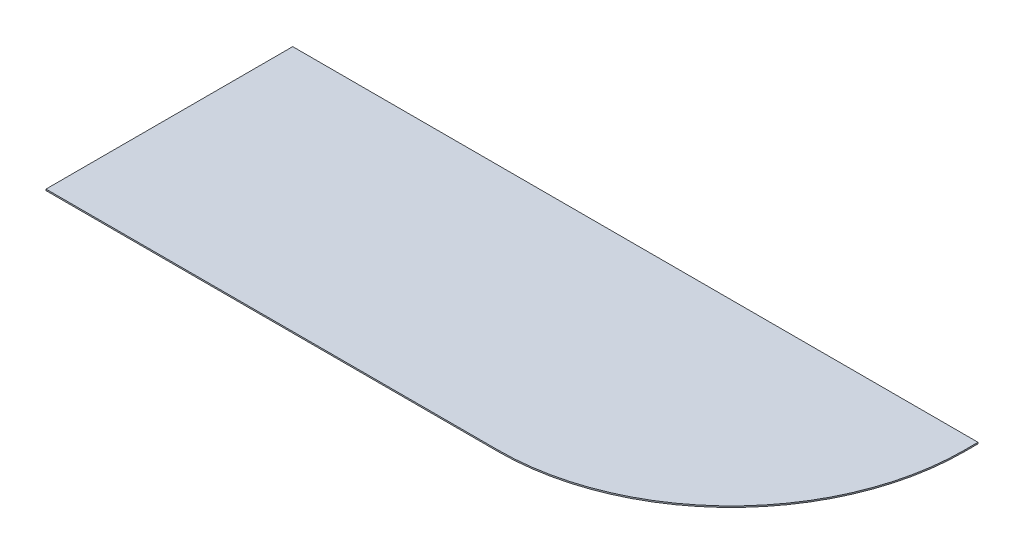
SolidWorks part; units mm, degrees
ref_plane "Front Plane" through (0, 0, 0) normal (0, 0, 1) x (1, 0, 0)
ref_plane "Top Plane" through (0, 0, 0) normal (0, 1, 0) x (1, 0, 0)
ref_plane "Right Plane" through (0, 0, 0) normal (1, 0, 0) x (0, 0, -1)
sketch "Sketch1" plane through (0, 0, 0) normal (0, 1, 0) x (1, 0, 0)
  line L1 (0, 0) -> (-500, 0)
  line L2 (0, 0) -> (0, -10)
  line L3 (-170, -180) -> (-500, -180)
  line L4 (-500, 0) -> (-500, -180)
  arc A0 (0, -10) -> (-170, -180) centre (-170, -10) cw
  dimension "D3" = 170
  dimension "D1" = 500
  dimension "D2" = 180
extrude "wing" add sketch "Sketch1" along normal blind 1
